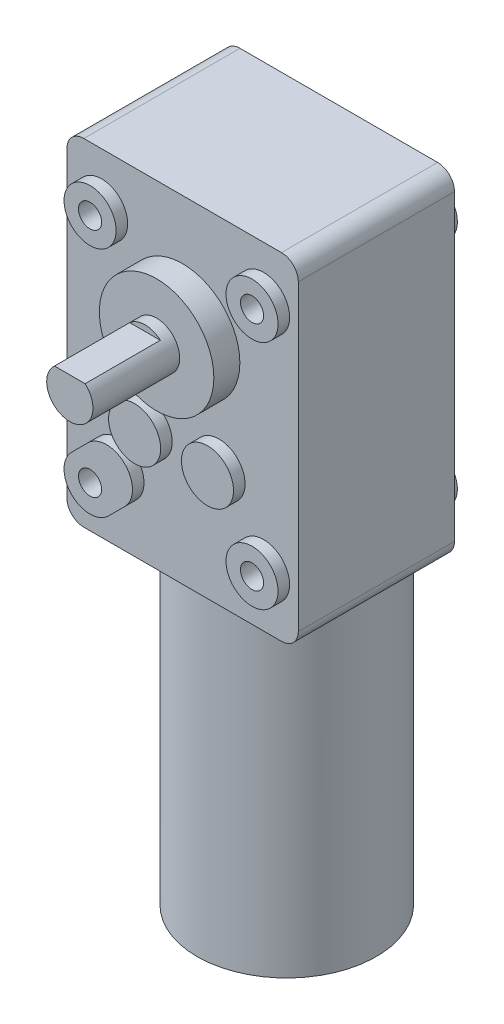
SolidWorks part; units mm, degrees
ref_plane "Front Plane" through (0, 0, 0) normal (0, 0, 1) x (1, 0, 0)
ref_plane "Top Plane" through (0, 0, 0) normal (0, 1, 0) x (1, 0, 0)
ref_plane "Right Plane" through (0, 0, 0) normal (1, 0, 0) x (0, 0, -1)
ref_plane "Plane1" through (0, 0, 171) normal (0, 0, -1) x (-1, 0, 0)
sketch "Sketch1" plane through (0, 0, 171) normal (0, 0, -1) x (-1, 0, 0)
  line L0 (-172.2191, 108.3324) -> (-172.2191, 50.1324)
  line L1 (-172.2191, 50.1324) -> (-132.2191, 50.1324)
  line L2 (-132.2191, 50.1324) -> (-132.2191, 108.3324)
  line L3 (-132.2191, 108.3324) -> (-172.2191, 108.3324)
extrude "Boss-Extrude1" add sketch "Sketch1" against normal blind 27
sketch "Sketch2" plane through (0, 50.1324, 0) normal (0, -1, 0) x (1, 0, 0)
  circle A0 centre (152.2191, 180) radius 15.5
extrude "Boss-Extrude2" add sketch "Sketch2" along normal blind 57
sketch "Sketch3" plane through (0, 0, 198) normal (0, 0, 1) x (1, 0, 0)
  line L0 (132.2191, 108.3324) -> (172.2191, 108.3324) construction
  circle A0 centre (152.2191, 88.2324) radius 9.9
  dimension "D1" = 20.1
extrude "Boss-Extrude3" add sketch "Sketch3" along normal blind 4.5
sketch "Sketch4" plane through (0, 0, 202.5) normal (0, 0, 1) x (1, 0, 0)
  line L0 (132.2191, 108.3324) -> (172.2191, 108.3324) construction
  circle A0 centre (152.2191, 88.2324) radius 4
  dimension "D1" = 20.1
extrude "Boss-Extrude4" add sketch "Sketch4" along normal blind 15
sketch "Sketch5" plane through (0, 0, 217.5) normal (0, 0, 1) x (1, 0, 0)
  line L0 (149.5734, 91.2324) -> (154.8649, 91.2324)
  line L1 (132.2191, 108.3324) -> (172.2191, 108.3324) construction
  arc A0 (154.8649, 91.2324) -> (149.5734, 91.2324) centre (152.2191, 88.2324) ccw
  dimension "D1" = 20.1
  dimension "D2" = 3
extrude "Cut-Extrude1" cut sketch "Sketch5" against normal blind 13
sketch "Sketch6" plane through (0, 0, 198) normal (0, 0, 1) x (1, 0, 0)
  line L0 (135.0372, 62.3144) -> (137.8656, 65.1428)
  line L1 (144.2296, 58.7789) -> (141.4011, 55.9505)
  arc A0 (141.4011, 55.9505) -> (135.0372, 62.3144) centre (138.2191, 59.1324) cw
  arc A1 (137.8656, 65.1428) -> (144.2296, 58.7789) centre (141.0476, 61.9609) cw
extrude "Boss-Extrude5" add sketch "Sketch6" along normal blind 2
sketch "Sketch7" plane through (0, 0, 171) normal (0, 0, -1) x (-1, 0, 0)
  arc A0 (-142.4838, 57.6962) -> (-136.7829, 63.3971) centre (-141.0476, 61.9609) cw
  arc A1 (-136.7829, 63.3971) -> (-142.4838, 57.6962) centre (-138.2191, 59.1324) cw
extrude "Boss-Extrude6" add sketch "Sketch7" along normal blind 2
sketch "Sketch8" plane through (0, -6.8676, 0) normal (0, -1, 0) x (1, 0, 0)
  line L0 (158.2126, 179.7188) -> (158.1599, 179.1588)
  arc A0 (158.1599, 179.1588) -> (158.2126, 179.7188) centre (152.2191, 180) cw
extrude "Boss-Extrude7" add sketch "Sketch8" along normal blind 2
ref_plane "Plane2" through (0, 59.1324, 0) normal (0, -1, 0) x (1, 0, 0)
sketch "Sketch9" plane through (0, 59.1324, 0) normal (0, -1, 0) x (1, 0, 0)
  line L0 (170.7191, 171) -> (166.2191, 171)
  line L1 (166.2191, 171) -> (166.2191, 169)
  line L2 (166.2191, 169) -> (170.7191, 169)
  line L3 (170.7191, 169) -> (170.7191, 171)
  line L4 (166.2191, 171) -> (166.2191, 169) construction
revolve "Revolve1" add sketch "Sketch9" angle 360 about L4
ref_plane "Plane3" through (0, 99.1324, 0) normal (0, -1, 0) x (1, 0, 0)
sketch "Sketch10" plane through (0, 99.1324, 0) normal (0, -1, 0) x (1, 0, 0)
  line L0 (142.7191, 171) -> (138.2191, 171)
  line L1 (138.2191, 171) -> (138.2191, 169)
  line L2 (138.2191, 169) -> (142.7191, 169)
  line L3 (142.7191, 169) -> (142.7191, 171)
  line L4 (138.2191, 171) -> (138.2191, 169) construction
revolve "Revolve2" add sketch "Sketch10" angle 360 about L4
ref_plane "Plane4" through (0, 70.5324, 0) normal (0, -1, 0) x (1, 0, 0)
sketch "Sketch11" plane through (0, 70.5324, 0) normal (0, -1, 0) x (1, 0, 0)
  line L0 (163.0191, 171) -> (158.5191, 171)
  line L1 (158.5191, 171) -> (158.5191, 169)
  line L2 (158.5191, 169) -> (163.0191, 169)
  line L3 (163.0191, 169) -> (163.0191, 171)
  line L4 (158.5191, 171) -> (158.5191, 169) construction
revolve "Revolve3" add sketch "Sketch11" angle 360 about L4
sketch "Sketch12" plane through (0, 99.1324, 0) normal (0, -1, 0) x (1, 0, 0)
  line L0 (170.7191, 171) -> (166.2191, 171)
  line L1 (166.2191, 171) -> (166.2191, 169)
  line L2 (166.2191, 169) -> (170.7191, 169)
  line L3 (170.7191, 169) -> (170.7191, 171)
  line L4 (166.2191, 171) -> (166.2191, 169) construction
revolve "Revolve4" add sketch "Sketch12" angle 360 about L4
sketch "Sketch13" plane through (0, 70.5324, 0) normal (0, -1, 0) x (1, 0, 0)
  line L0 (150.4191, 171) -> (145.9191, 171)
  line L1 (145.9191, 171) -> (145.9191, 169)
  line L2 (145.9191, 169) -> (150.4191, 169)
  line L3 (150.4191, 169) -> (150.4191, 171)
  line L4 (145.9191, 171) -> (145.9191, 169) construction
revolve "Revolve5" add sketch "Sketch13" angle 360 about L4
ref_plane "Plane5" through (0, 88.2324, 0) normal (0, -1, 0) x (1, 0, 0)
sketch "Sketch14" plane through (0, 88.2324, 0) normal (0, -1, 0) x (1, 0, 0)
  line L0 (162.1191, 171) -> (152.2191, 171)
  line L1 (152.2191, 171) -> (152.2191, 166.5)
  line L2 (152.2191, 166.5) -> (162.1191, 166.5)
  line L3 (162.1191, 166.5) -> (162.1191, 171)
  line L4 (152.2191, 171) -> (152.2191, 166.5) construction
revolve "Revolve6" add sketch "Sketch14" angle 360 about L4
ref_plane "Plane6" through (0, 59.3324, 0) normal (0, 1, 0) x (1, 0, 0)
sketch "Sketch15" plane through (0, 59.3324, 0) normal (0, 1, 0) x (1, 0, 0)
  line L0 (170.7191, -198) -> (166.2191, -198)
  line L1 (166.2191, -198) -> (166.2191, -200)
  line L2 (166.2191, -200) -> (170.7191, -200)
  line L3 (170.7191, -200) -> (170.7191, -198)
  line L4 (166.2191, -198) -> (166.2191, -200) construction
revolve "Revolve7" add sketch "Sketch15" angle 360 about L4
ref_plane "Plane7" through (0, 99.3324, 0) normal (0, 1, 0) x (1, 0, 0)
sketch "Sketch16" plane through (0, 99.3324, 0) normal (0, 1, 0) x (1, 0, 0)
  line L0 (170.7191, -198) -> (166.2191, -198)
  line L1 (166.2191, -198) -> (166.2191, -200)
  line L2 (166.2191, -200) -> (170.7191, -200)
  line L3 (170.7191, -200) -> (170.7191, -198)
  line L4 (166.2191, -198) -> (166.2191, -200) construction
revolve "Revolve8" add sketch "Sketch16" angle 360 about L4
ref_plane "Plane8" through (0, 70.5324, 0) normal (0, 1, 0) x (1, 0, 0)
sketch "Sketch17" plane through (0, 70.5324, 0) normal (0, 1, 0) x (1, 0, 0)
  line L0 (163.0191, -198) -> (158.5191, -198)
  line L1 (158.5191, -198) -> (158.5191, -200)
  line L2 (158.5191, -200) -> (163.0191, -200)
  line L3 (163.0191, -200) -> (163.0191, -198)
  line L4 (158.5191, -198) -> (158.5191, -200) construction
revolve "Revolve9" add sketch "Sketch17" angle 360 about L4
sketch "Sketch18" plane through (0, 99.3324, 0) normal (0, 1, 0) x (1, 0, 0)
  line L0 (142.7191, -198) -> (138.2191, -198)
  line L1 (138.2191, -198) -> (138.2191, -200)
  line L2 (138.2191, -200) -> (142.7191, -200)
  line L3 (142.7191, -200) -> (142.7191, -198)
  line L4 (138.2191, -198) -> (138.2191, -200) construction
revolve "Revolve10" add sketch "Sketch18" angle 360 about L4
sketch "Sketch19" plane through (0, 70.5324, 0) normal (0, 1, 0) x (1, 0, 0)
  line L0 (150.4191, -198) -> (145.9191, -198)
  line L1 (145.9191, -198) -> (145.9191, -200)
  line L2 (145.9191, -200) -> (150.4191, -200)
  line L3 (150.4191, -200) -> (150.4191, -198)
  line L4 (145.9191, -198) -> (145.9191, -200) construction
revolve "Revolve11" add sketch "Sketch19" angle 360 about L4
fillet "Fillet1" radius 2.913 4 edges at (132.2191, 108.3324, 184.5) (172.2191, 108.3324, 184.5) (172.2191, 50.1324, 184.5) (132.2191, 50.1324, 184.5)
sketch "Sketch20" plane through (0, 0, 200) normal (0, 0, 1) x (1, 0, 0)
  line L0 (138.2191, 99.3324) -> (166.2191, 99.3324) construction
  line L1 (166.2191, 99.3324) -> (166.2191, 59.3324) construction
  line L2 (166.2191, 59.3324) -> (138.2191, 59.3324) construction
  line L3 (138.2191, 59.3324) -> (138.2191, 99.3324) construction
  circle A0 centre (138.2191, 99.3324) radius 2
  circle A1 centre (166.2191, 99.3324) radius 2
  circle A2 centre (138.2191, 59.3324) radius 2
  circle A3 centre (166.2191, 59.3324) radius 2
  dimension "D1" = 4
  dimension "D2" = 4
  dimension "D3" = 4
  dimension "D4" = 4
extrude "Cut-Extrude2" cut sketch "Sketch20" against normal blind 5
